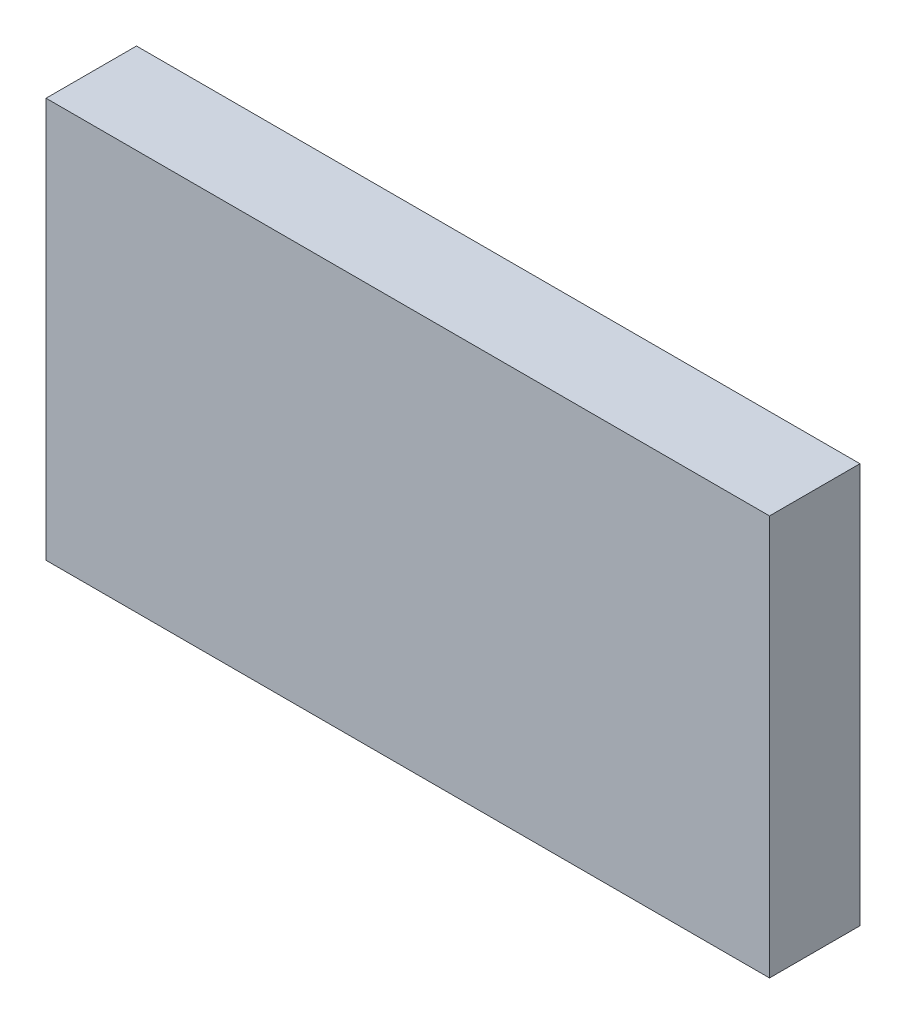
SolidWorks part; units mm, degrees
ref_plane "Front Plane" through (0, 0, 0) normal (0, 0, 1) x (1, 0, 0)
ref_plane "Top Plane" through (0, 0, 0) normal (0, 1, 0) x (1, 0, 0)
ref_plane "Right Plane" through (0, 0, 0) normal (1, 0, 0) x (0, 0, -1)
sketch "Sketch1" plane through (0, 0, 0) normal (0, 1, 0) x (1, 0, 0)
  line L1 (-101.6, 11.3974) -> (0, 11.3974)
  line L2 (-101.6, 11.3974) -> (-101.6, -1.3026)
  line L3 (-101.6, -1.3026) -> (0, -1.3026)
  line L4 (0, 11.3974) -> (0, -1.3026)
  dimension "D1" = 12.7
  dimension "D2" = 101.6
extrude "Boss-Extrude1" add sketch "Sketch1" along normal blind 56.2
sketch "Sketch2" plane through (0, 0, 0) normal (0, -1, 0) x (1, 0, 0)
  line L0 (-76.2, 1.3026) -> (-76.2, -11.3974) construction
  line L1 (-101.6, 1.3026) -> (0, 1.3026) construction
  line L2 (0, -11.3974) -> (-101.6, -11.3974) construction
  line L3 (-63.5, 1.3026) -> (-63.5, -11.3974) construction
  line L4 (-88.9, 1.3026) -> (-88.9, -11.3974) construction
  line L5 (-101.6, -11.3974) -> (-101.6, 1.3026) construction
  line L6 (-101.6, 1.3026) -> (-88.9, -11.3974) construction
  line L7 (-88.9, -11.3974) -> (-76.2, 1.3026) construction
  line L8 (-76.2, 1.3026) -> (-63.5, -11.3974) construction
  point P13 (-95.25, -5.0474)
  point P15 (-82.55, -5.0474)
  point P16 (-69.85, -5.0474)
  dimension "D1" = 12.7
  dimension "D2" = 12.7
  dimension "D3" = 12.7
